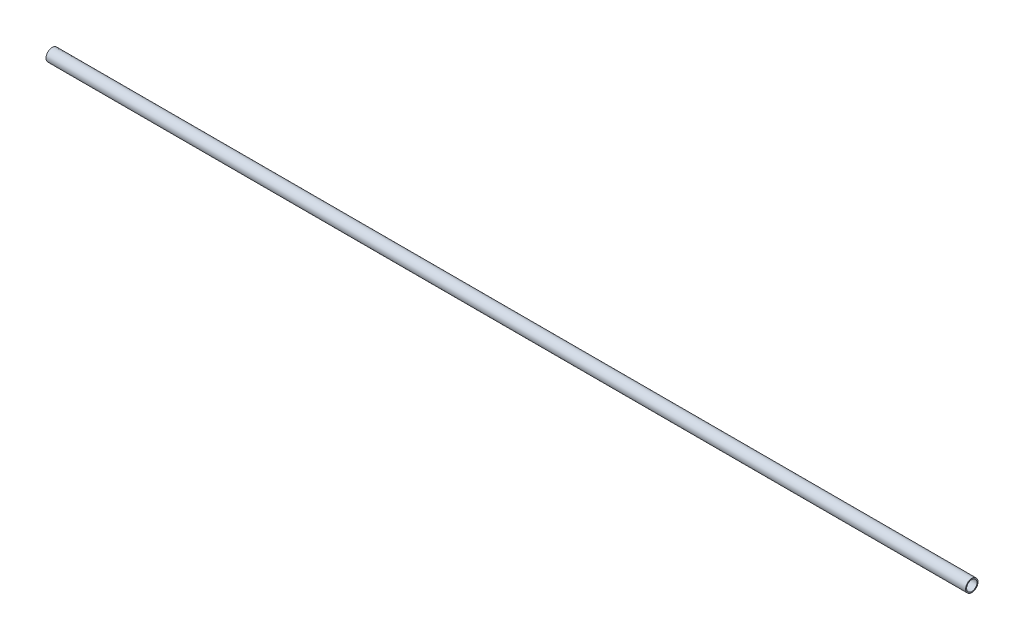
SolidWorks part; units mm, degrees
ref_plane "Front Plane" through (0, 0, 0) normal (0, 0, 1) x (1, 0, 0)
ref_plane "Top Plane" through (0, 0, 0) normal (0, 1, 0) x (1, 0, 0)
ref_plane "Right Plane" through (0, 0, 0) normal (1, 0, 0) x (0, 0, -1)
sketch "Sketch1" plane through (0, 0, 0) normal (1, 0, 0) x (0, 0, -1)
  circle A0 centre (0, 0) radius 3.175
  circle A1 centre (0, 0) radius 2.667
  dimension "D1" = 6.35
  dimension "D2" = 0.508
extrude "Boss-Extrude1" add sketch "Sketch1" against normal blind 472.313
move or copy body "Body-Move/Copy1" [suppressed] bodies to move or copy 101 parameters "D1"=0, "D2"=0, "D3"=0
